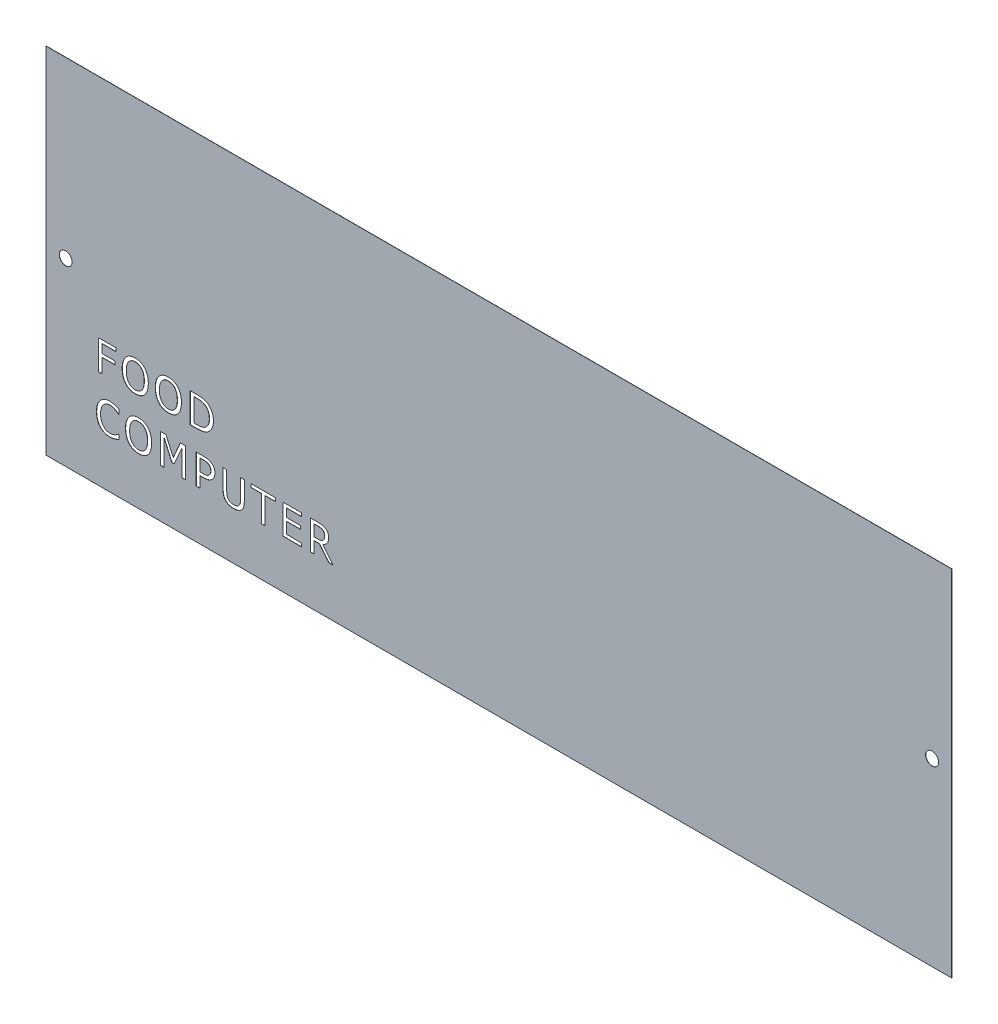
SolidWorks part; units mm, degrees
material "Custom Plastic"
ref_plane "Front Plane" through (0, 0, 0) normal (0, 0, 1) x (1, 0, 0)
ref_plane "Top Plane" through (0, 0, 0) normal (0, 1, 0) x (1, 0, 0)
ref_plane "Right Plane" through (0, 0, 0) normal (1, 0, 0) x (0, 0, -1)
sketch "Sketch1" plane through (0, 0, 0) normal (0, 0, 1) x (1, 0, 0)
  line L1 (292.1, -114.3) -> (-292.1, -114.3)
  line L2 (292.1, -114.3) -> (292.1, 114.3)
  line L3 (292.1, 114.3) -> (-292.1, 114.3)
  line L4 (-292.1, -114.3) -> (-292.1, 114.3)
  line L5 (292.1, -114.3) -> (-292.1, 114.3) construction
  line L6 (292.1, 114.3) -> (-292.1, -114.3) construction
  point P0 (0, 0)
extrude "Boss-Extrude1" add sketch "Sketch1" along normal blind 0.127
sketch "Sketch3" plane through (0, 0, 0.127) normal (0, 0, 1) x (1, 0, 0)
  line L0 (292.1, -114.3) -> (292.1, 114.3) construction
  line L2 (0, 449.0266) -> (0, -490.5745) construction
  line L3 (-292.1, -114.3) -> (292.1, -114.3) construction
  circle A1 centre (-279.5016, 2.0066) radius 4.1656
  circle A2 centre (279.5016, 2.0066) radius 4.1656
extrude "Cut-Extrude1" cut sketch "Sketch3" against normal through all
sketch "Sketch2" plane through (0, 0, 0.127) normal (0, 0, 1) x (1, 0, 0)
  text T0 "OpenAG Personal Food Computer" font "Tahoma" height in points 72
extrude "Text" [suppressed] cut sketch "Sketch2" against normal blind 1.27
sketch "Sketch4" plane through (0, 0, 0.127) normal (0, 0, 1) x (1, 0, 0)
  line L0 (-260.35, -50.8) -> (67.6197, -50.8) construction
  line L2 (-292.1, -114.3) -> (292.1, -114.3) construction
  line L3 (-292.1, 114.3) -> (-292.1, -114.3) construction
  text T0 "FOOD\r\nCOMPUTER" font "Tahoma" height 19.05
  dimension "D1" = 63.5
  dimension "D2" = 31.75
extrude "Cut-Extrude2" cut sketch "Sketch4" against normal up to next
equation "\"Height\"= 32in"
equation "\"Width\"= 23in"
equation "\"Depth\"= 20in"
equation "\"Plexi\"= .121in"
equation "\"MagnetThickness\"= 0.125in"
equation "\"MagnetDiameter\"= 12mm"
equation "\"DoorPlexi\" = \"Plexi\""
equation "\"BasePlateThickness\" = 0.5in"
equation "\"BasePlateWidth\" = \"Width\"+\"EBWidth\"-2*\"Plexi\""
equation "\"BasePlateDepth\" = \"TopBarDepth\"+2*\"CornerCube\""
equation "\"Boxsize\" = .75in"
equation "\"Boxinner\" = .625in"
equation "\"CornerCube\" = 0.75in"
equation "\"FingerLength\" = 1.125in"
equation "\"FingerWidth\" = .625in"
equation "\"Cutwidth\"= .016in"
equation "\"Earsize\"= 1in + \"Cutwidth\" /2"
equation "\"Slotsize\" = 1in - \"CutWidth\" / 2"
equation "\"InnerWidth\" = \"Width\" - 2* \"Plexi\""
equation "\"InnerHeight\" = \"Height\" -2 * \"Plexi\""
equation "\"InnerDepth\" = \"Depth\" - 2*\"Plexi\""
equation "\"RearNumHoles\" = 4"
equation "\"RearHolesBorder\" = 2.25"
equation "\"RearHoleSpacing\" = (\"Width\" - 2*\"RearHolesBorder\") / (\"RearNumHoles\"-1)"
equation "\"RearBarLength\" = (\"InnerWidth\"-2*\"CornerCube\")"
equation "\"RearTopNumHoles\" = 4"
equation "\"RearTopHolesBorder\" = 3.1"
equation "\"RearTopHolesSpacing\" = (\"Width\" - 2*\"RearTopHolesBorder\") / (\"RearTopNumHoles\"-1)"
equation "\"SideTopNumHoles\" = 4"
equation "\"SideTopHoleOffset\"=\"CornerCube\"+\"FingerLength\"+\"Plexi\"+.5"
equation "\"SideTopHoleSpacing\" = (\"TopBarDepth\"-2*\"SideTopHoleOffset\") / (\"SideTopNumHoles\"-1)"
equation "\"SideHorizNumHoles\" = 4"
equation "\"SideHorizHoleBorder\" = 1.50"
equation "\"SideHorizHoleSpacing\" = (\"TopBarDepth\"-2*\"SideHorizHoleBorder\") / (\"SideHorizNumHoles\"-1)"
equation "\"SideVertBarLength\"=\"Height\"-\"BasePlateThickness\"-2*\"CornerCube\"-\"Plexi\""
equation "\"SideVertNumHoles\" = 4"
equation "\"SideVertHolesBorder\" = \"CornerCube\"+\"FingerLength\"+1.50"
equation "\"SideVertHoleSpacing\" = (\"InnerHeight\" - 2*\"SideVertHolesBorder\") / (\"SideVertNumHoles\"-1)"
equation "\"RearSideVertNumHoles\" = 4"
equation "\"RearSideVertHolesBorder\" = 2.4"
equation "\"RearSideVertHoleSpacing\" = (\"InnerHeight\" - 2*\"RearSideVertHolesBorder\") / (\"RearSideVertNumHoles\"-1)"
equation "\"RivetDia\" = .228in"
equation "\"SlotDepth\" = \"Plexi\" + 0.75in + .005in"
equation "\"SideSlotWidth\"   = \"Plexi\"+.005in"
equation "\"SidePanelVertSpacing\" = (\"Height\"-2*(1.75-\"Plexi\")) / 5"
equation "\"BottomPanelSideHoleSpacing\" = (\"InnerDepth\"-2*(1.75-\"Plexi\")) / 4"
equation "\"FrontDoorGap\" = .1in"
equation "\"TopDepth\" = \"Depth\"-\"DoorPlexi\"-\"FrontDoorGap\""
equation "\"TopBarDepth\" = \"Depth\"-\"DoorPlexi\"-\"Plexi\"-2*\"MagnetThickness\"-2*\"CornerCube\""
equation "\"D1@Sketch1\"=\"Width\""
equation "\"D1@Boss-Extrude1\"=\"DoorPlexi\""
equation "\"EBWidth\" = 9in"
equation "\"ComponentMountDia\"=0.1770"
equation "\"ShelfThickness\" = .1250in"
equation "\"BoxsizeHalf\" = \"Boxsize\"/2"
equation "\"Rivet3_16Dia\" = .191in"
equation "\"BinderPostDia\" = .228in"
equation "\"CoolerDepth\" = 12in"
equation "\"ShelfGap\" = 0.5in"
equation "\"ShelfDepth\" = \"TopBarDepth\"+\"CornerCube\"-\"CoolerDepth\""
equation "\"ShelfBarDepth\"=\"ShelfDepth\"-2*\"CornerCube\""
equation "\"ShelfWidth\" = \"EBWidth\"-\"ShelfGap\""
equation "\"ShelfBarWidth\" = \"EBWidth\"-\"Boxsize\""
equation "\"ShelfBarWidthShort\" = \"ShelfBarWidth\"-\"Boxsize\"-\"ShelfGap\""
equation "\"ShelfHeight1\" = 13in"
equation "\"ShelfHeight2\" = 24in"
equation "\"IntakeWidth\"=4in"
equation "\"IntakeHeight\"=2in"
equation "\"ExhaustWidth\"=4in"
equation "\"ExhaustHeight\"=2in"
equation "\"VentSpacing\"=7in"
equation "\"VentVertLocation\"=12.75in"
equation "\"AngleBracketLengthShort\"=.625in"
equation "\"AngleBracketLengthLong\"=1in"
equation "\"AngleBracketWidth\"=.5in"
equation "\"AngleBracketThickness\"=.125in"
equation "\"AngleBracketHolePosShort\"=.358in"
equation "\"AngleBracketHolePosLong\"=.7in"
equation "\"AngleBracketHoleDia\"=\"Rivet3_16Dia\""
equation "\"ShelfBarAngleHole\"=\"ShelfGap\"+\"Boxsize\"+\"AngleBracketHolePosShort\""
equation "\"PSBracketThickness\" = .0641in"
equation "\"EBForwardMountOffset\" = 4.0in"
equation "\"EBForwardMount\" = 2*\"Boxsize\"+\"CoolerDepth\"+\"EBForwardMountOffset\""
equation "\"EBRearwardMountOffset\" = 1.5in"
equation "\"EBRearwardMount\"= \"Boxsize\"+\"EBRearwardMountOffset\""
equation "\"MagSealWidth\" = \"InnerWidth\""
equation "\"MagSealHeight\" = \"Height\"-\"BasePlateThickness\"-\"Plexi\""
equation "\"MagWidth\" = .500in"
equation "\"SiliconeSealOD\" = .3125in"
equation "\"SiliconeSealID\" = .1875in"
equation "\"SiliconeSealWidth\" = \"MagSealWidth\" - 2*\"MagWidth\"-\"SiliconeSealOD\""
equation "\"SiliconeSealHeigth\" = \"MagSealHeight\" - 2*\"MagWidth\"-\"SiliconeSealOD\""
equation "\"HooknLoopThick\" = .085in"
equation "\"HooknLoopWidth\" = 0.75in"
equation "\"HooknLoopHeigth\" = 0.75in"
equation "\"D4@Sketch3\"=\"BasePlateThickness\"+\"Boxsize\"+3.329"
equation "\"D5@Sketch3\"=\"RivetDia\"+.1"
equation "\"D1@Sketch3\"=\"Plexi\"+\"BoxsizeHalf\""
